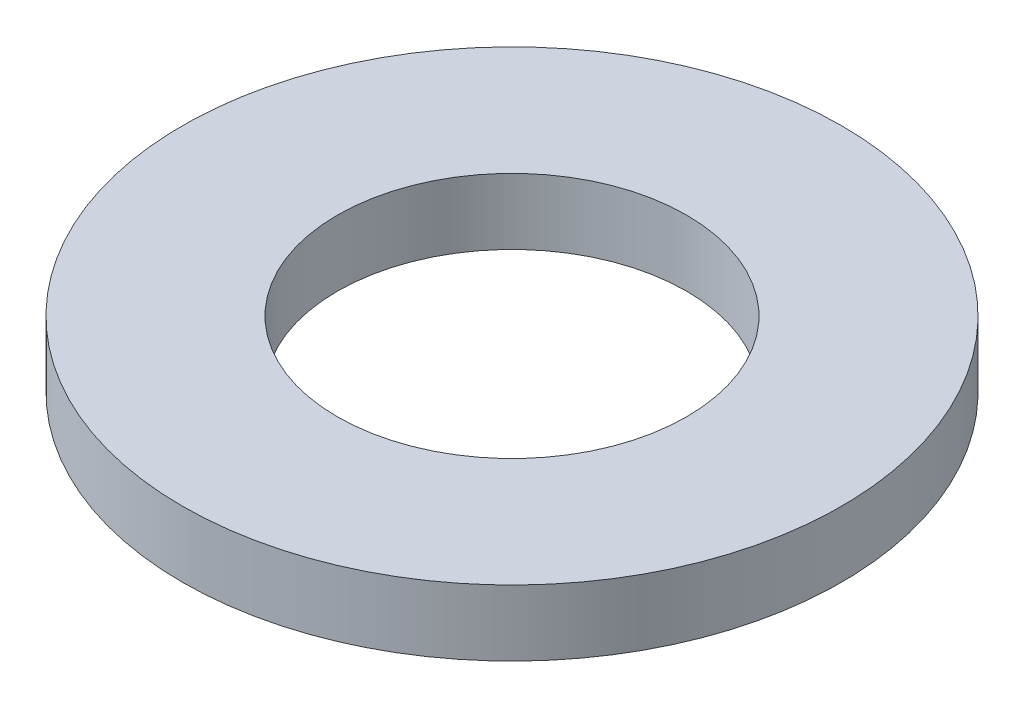
SolidWorks part; units mm, degrees
ref_plane "Płaszczyzna XY" through (0, 0, 0) normal (0, 0, 1) x (1, 0, 0)
ref_plane "Płaszczyzna XZ" through (0, 0, 0) normal (0, 1, 0) x (1, 0, 0)
ref_plane "Płaszczyzna YZ" through (0, 0, 0) normal (1, 0, 0) x (0, 0, -1)
sketch "Szkic1" plane through (0, 0, 0) normal (0, 1, 0) x (1, 0, 0)
  circle A0 centre (0, 0) radius 2.65
  circle A1 centre (0, 0) radius 5
  dimension "D1" = 10
  dimension "D2" = 5.3
extrude "Dodanie-wyciągnięcie1" add sketch "Szkic1" along normal blind 1
